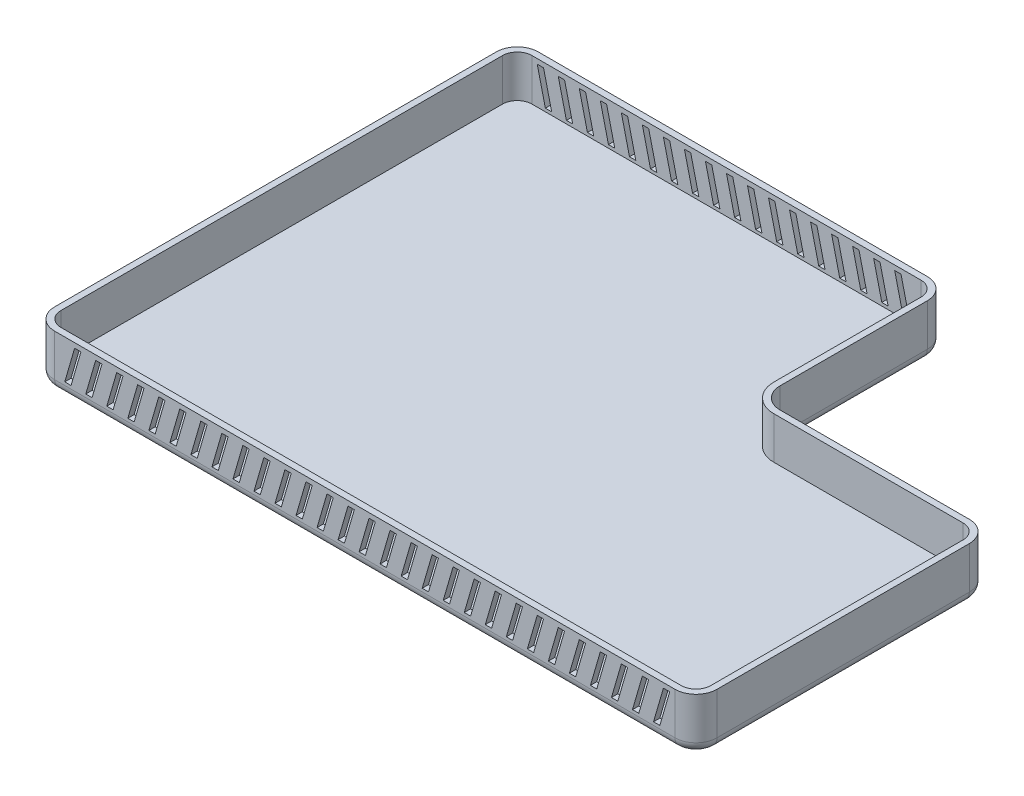
SolidWorks part; units mm, degrees
material "Chrome Stainless Steel"
ref_plane "Front Plane" through (0, 0, 0) normal (0, 0, 1) x (1, 0, 0)
ref_plane "Top Plane" through (0, 0, 0) normal (0, 1, 0) x (1, 0, 0)
ref_plane "Right Plane" through (0, 0, 0) normal (1, 0, 0) x (0, 0, -1)
sketch "Sketch1" plane through (0, 0, 0) normal (0, 1, 0) x (1, 0, 0)
  line L0 (305, 140) -> (215, 140)
  line L1 (10, 0) -> (305, 0)
  line L2 (0, 10) -> (0, 220)
  line L3 (10, 230) -> (195, 230)
  line L4 (315, 10) -> (315, 130)
  line L5 (205, 150) -> (205, 220)
  arc A0 (10, 0) -> (0, 10) centre (10, 10) cw
  arc A1 (305, 0) -> (315, 10) centre (305, 10) ccw
  arc A2 (305, 140) -> (315, 130) centre (305, 130) cw
  arc A3 (215, 140) -> (205, 150) centre (215, 150) cw
  arc A4 (205, 220) -> (195, 230) centre (195, 220) ccw
  arc A5 (0, 220) -> (10, 230) centre (10, 220) cw
  point P9 (0, 0)
  point P12 (315, 0)
  point P15 (315, 140)
  point P18 (205, 140)
  dimension "D2" = 10
  dimension "D1" = 315
  dimension "D3" = 90
  dimension "D4" = 110
  dimension "D5" = 230
extrude "Boss-Extrude1" add sketch "Sketch1" along normal blind 5
sketch "Sketch3" plane through (0, 0, 0) normal (0, 1, 0) x (1, 0, 0)
  line L24 (10, 3) -> (305, 3)
  line L25 (312, 10) -> (312, 130)
  line L26 (305, 137) -> (215, 137)
  line L27 (202, 150) -> (202, 220)
  line L28 (195, 227) -> (10, 227)
  line L29 (3, 220) -> (3, 10)
  line L30 (10, 3) -> (305, 3)
  line L31 (312, 10) -> (312, 130)
  line L32 (305, 137) -> (215, 137)
  line L33 (202, 150) -> (202, 220)
  line L34 (195, 227) -> (10, 227)
  line L35 (3, 220) -> (3, 10)
  line L36 (10, 0) -> (305, 0)
  line L37 (315, 10) -> (315, 130)
  line L38 (305, 140) -> (215, 140)
  line L39 (205, 150) -> (205, 220)
  line L40 (195, 230) -> (10, 230)
  line L41 (0, 220) -> (0, 10)
  line L42 (10, 0) -> (305, 0)
  line L43 (315, 10) -> (315, 130)
  line L44 (305, 140) -> (215, 140)
  line L45 (205, 150) -> (205, 220)
  line L46 (195, 230) -> (10, 230)
  line L47 (0, 220) -> (0, 10)
  arc A25 (305, 3) -> (312, 10) centre (305, 10) ccw
  arc A26 (312, 130) -> (305, 137) centre (305, 130) ccw
  arc A27 (202, 150) -> (215, 137) centre (215, 150) ccw
  arc A28 (202, 220) -> (195, 227) centre (195, 220) ccw
  arc A29 (10, 227) -> (3, 220) centre (10, 220) ccw
  arc A30 (3, 10) -> (10, 3) centre (10, 10) ccw
  arc A31 (305, 3) -> (312, 10) centre (305, 10) ccw
  arc A32 (312, 130) -> (305, 137) centre (305, 130) ccw
  arc A33 (202, 150) -> (215, 137) centre (215, 150) ccw
  arc A34 (202, 220) -> (195, 227) centre (195, 220) ccw
  arc A35 (10, 227) -> (3, 220) centre (10, 220) ccw
  arc A36 (3, 10) -> (10, 3) centre (10, 10) ccw
  arc A37 (305, 0) -> (315, 10) centre (305, 10) ccw
  arc A38 (315, 130) -> (305, 140) centre (305, 130) ccw
  arc A39 (205, 150) -> (215, 140) centre (215, 150) ccw
  arc A40 (205, 220) -> (195, 230) centre (195, 220) ccw
  arc A41 (10, 230) -> (0, 220) centre (10, 220) ccw
  arc A42 (0, 10) -> (10, 0) centre (10, 10) ccw
  arc A43 (305, 0) -> (315, 10) centre (305, 10) ccw
  arc A44 (315, 130) -> (305, 140) centre (305, 130) ccw
  arc A45 (205, 150) -> (215, 140) centre (215, 150) ccw
  arc A46 (205, 220) -> (195, 230) centre (195, 220) ccw
  arc A47 (10, 230) -> (0, 220) centre (10, 220) ccw
  arc A48 (0, 10) -> (10, 0) centre (10, 10) ccw
  dimension "D1" = 3
  dimension "D2" = 0
extrude "Boss-Extrude2" add sketch "Sketch3" along normal blind 25
fillet "Fillet1" radius 5 12 edges at (157.5, 0, 0) (312.0711, 0, -2.9289) (315, 0, -70) (312.0711, 0, -137.0711) (260, 0, -140) (207.9289, 0, -142.9289) (205, 0, -185) (202.0711, 0, -227.0711) (102.5, 0, -230) (2.9289, 0, -227.0711) (0, 0, -115) (2.9289, 0, -2.9289)
sketch "Sketch4" plane through (0, 0, 0) normal (0, 0, 1) x (1, 0, 0)
  line L0 (297.7992, 6.5) -> (294.7992, 6.5)
  line L1 (297.7992, 6.5) -> (302.5, 22.7007)
  line L2 (294.7992, 6.5) -> (299.5, 22.7007)
  line L3 (302.5, 22.7007) -> (299.5, 22.7007)
  line L4 (10, 5) -> (305, 5) construction
  line L5 (305, 25) -> (305, 5) construction
  dimension "D1" = 3
  dimension "D2" = 1.5
  dimension "D3" = 2.5
extrude "Cut-Extrude1" cut sketch "Sketch4" against normal blind 10 contours L2 L3 L1 L0
pattern_linear "LPattern1" count 29 spacing 10 along (-1, 0, 0) of "Cut-Extrude1"
sketch "Sketch5" plane through (0, 0, -230) normal (0, 0, -1) x (-1, 0, 0)
  line L0 (-16.3709, 6.5) -> (-19.3709, 6.5)
  line L1 (-16.3709, 6.5) -> (-12.5, 22.7007)
  line L2 (-19.3709, 6.5) -> (-15.5, 22.7007)
  line L3 (-12.5, 22.7007) -> (-15.5, 22.7007)
  line L4 (-195, 5) -> (-10, 5) construction
  line L5 (-10, 25) -> (-10, 5) construction
  dimension "D1" = 1.5
  dimension "D2" = 2.5
  dimension "D3" = 3
extrude "Cut-Extrude2" cut sketch "Sketch5" against normal blind 10
pattern_linear "LPattern2" count 18 spacing 10 along (1, 0, 0) of "Cut-Extrude2"
